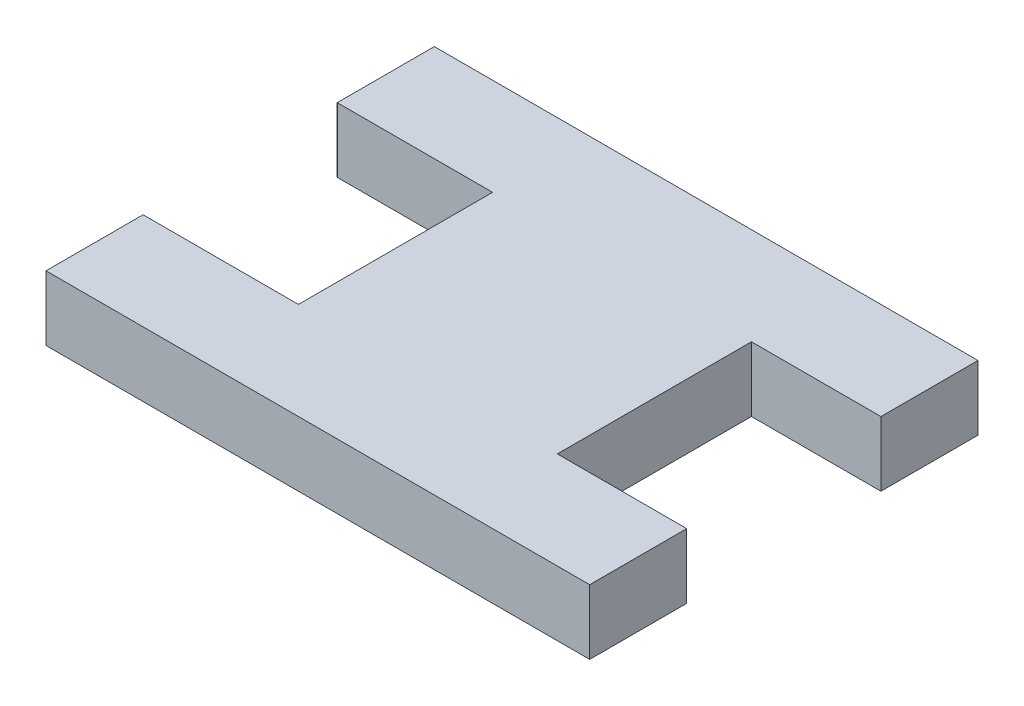
SolidWorks part; units mm, degrees
ref_plane "Front Plane" through (0, 0, 0) normal (0, 0, 1) x (1, 0, 0)
ref_plane "Top Plane" through (0, 0, 0) normal (0, 1, 0) x (1, 0, 0)
ref_plane "Right Plane" through (0, 0, 0) normal (1, 0, 0) x (0, 0, -1)
sketch "Sketch1" plane through (0, 0, 0) normal (0, 1, 0) x (1, 0, 0)
  line L1 (-47.5, -15) -> (47.5, -15)
  line L2 (-47.5, -15) -> (-47.5, 15)
  line L3 (-47.5, 15) -> (47.5, 15)
  line L4 (47.5, -15) -> (47.5, 15)
  line L5 (-47.5, -15) -> (47.5, 15) construction
  line L6 (-47.5, 15) -> (47.5, -15) construction
  circle A0 centre (-32.5, 0) radius 7
  circle A2 centre (-42.9, 0) radius 1
  circle A9 centre (-45.9, 0) radius 1
  circle A10 centre (-32.5, 10.4) radius 1
  circle A11 centre (-32.5, 13.4) radius 1
  circle A12 centre (-22.1, 0) radius 1
  circle A13 centre (-19.1, 0) radius 1
  circle A14 centre (-32.5, -10.4) radius 1
  circle A15 centre (-32.5, -13.4) radius 1
  point P0 (0, 0)
  point P26 (-32.5, 0)
  point P27 (-32.5, 0)
  dimension "D6" = 14
  dimension "D7" = 15
  dimension "D3" = 10.4
  dimension "D4" = 2
  dimension "D10" = 3
  dimension "D1" = 30
  dimension "D2" = 95
  dimension "D5" = 4
extrude "Boss-Extrude1" add sketch "Sketch1" along normal blind 5
sketch "Sketch3" plane through (0, 5, 0) normal (0, 1, 0) x (1, 0, 0)
  line L0 (-7.5, 5) -> (-2.5, 5)
  line L1 (-7.5, 5) -> (-7.5, -5)
  line L2 (-7.5, -5) -> (-2.5, -5)
  line L3 (-2.5, 5) -> (-2.5, -5)
  line L4 (-7.5, 5) -> (-2.5, -5) construction
  line L5 (-7.5, -5) -> (-2.5, 5) construction
  line L6 (-47.5, 15) -> (-47.5, -15) construction
  point P0 (-5, 0)
  dimension "D1" = 5
  dimension "D2" = 10
  dimension "D3" = 40
extrude "Cut-Extrude2" cut sketch "Sketch3" against normal blind 10
sketch "Sketch4" plane through (0, 5, 0) normal (0, 1, 0) x (1, 0, 0)
  line L0 (47.5, -15) -> (47.5, 15) construction
  line L1 (-3, -10) -> (37.5, -10) construction
  line L2 (-3, -10) -> (-3, 10) construction
  line L3 (-3, 10) -> (37.5, 10) construction
  line L4 (37.5, -10) -> (37.5, 10) construction
  line L5 (-3, -10) -> (37.5, 10) construction
  line L6 (-3, 10) -> (37.5, -10) construction
  line L7 (-2.5, 15) -> (-2.5, -15) construction
  line L8 (47.5, 15) -> (-47.5, 15) construction
  line L9 (-47.5, -15) -> (47.5, -15) construction
  circle A9 centre (-32.5, 0) radius 7 construction
  circle A10 centre (-32.5, 0) radius 7
  circle A15 centre (-32.5, -13.4) radius 1 construction
  circle A16 centre (-32.5, -10.4) radius 1 construction
  circle A17 centre (-42.9, 0) radius 1 construction
  circle A18 centre (-45.9, 0) radius 1 construction
  circle A19 centre (-32.5, 13.4) radius 1 construction
  circle A20 centre (-22.1, 0) radius 1 construction
  circle A21 centre (-19.1, 0) radius 1 construction
  circle A22 centre (-32.5, 10.4) radius 1 construction
  circle A23 centre (-32.5, -13.4) radius 1
  circle A24 centre (-32.5, -10.4) radius 1
  circle A25 centre (-42.9, 0) radius 1
  circle A26 centre (-45.9, 0) radius 1
  circle A27 centre (-32.5, 13.4) radius 1
  circle A28 centre (-22.1, 0) radius 1
  circle A29 centre (-19.1, 0) radius 1
  circle A30 centre (-32.5, 10.4) radius 1
  circle A31 centre (27.5, -13.4) radius 1
  circle A32 centre (27.5, -10.4) radius 1
  circle A33 centre (40.9, 0) radius 1
  circle A34 centre (37.9, 0) radius 1
  circle A35 centre (27.5, 0) radius 7
  circle A36 centre (27.5, 10.4) radius 1
  circle A37 centre (27.5, 13.4) radius 1
  circle A38 centre (17.1, 0) radius 1
  circle A39 centre (14.1, 0) radius 1
  point P0 (17.25, 0)
  point P29 (27.5, 0)
  dimension "D4" = 10
  dimension "D1" = 40.5
  dimension "D2" = 20
  dimension "D3" = 10
extrude "Cut-Extrude3" cut sketch "Sketch4" against normal blind 10
fillet "Fillet1" radius 10 4 edges at (47.5, 2.5, 15) (47.5, 2.5, -15) (-47.5, 2.5, 15) (-47.5, 2.5, -15)
sketch "Sketch5" plane through (0, 5, 0) normal (0, 1, 0) x (1, 0, 0)
  circle A0 centre (-7.5, 5) radius 2.05
  circle A1 centre (-2.5, 5) radius 2.05
  circle A2 centre (-2.5, -5) radius 2.05
  circle A3 centre (-7.5, -5) radius 2.05
  dimension "D1" = 4.1
extrude "Cut-Extrude4" cut sketch "Sketch5" against normal up to next
sketch "Sketch6" plane through (0, 5, 0) normal (0, 1, 0) x (1, 0, 0)
  line L0 (-22.5, 15) -> (19.5, 15)
  line L1 (37.5, 15) -> (-37.5, 15) construction
  line L2 (-22.5, 15) -> (-22.5, 7.5)
  line L3 (-22.5, 7.5) -> (-10.5, 7.5)
  line L4 (-10.5, 7.5) -> (-10.5, -7.5)
  line L5 (19.5, 15) -> (19.5, 7.5)
  line L6 (19.5, 7.5) -> (9.5, 7.5)
  line L7 (9.5, 7.5) -> (9.5, -7.5)
  line L8 (-10.5, 0) -> (9.5, 0) construction
  line L9 (19.5, -15) -> (19.5, -7.5)
  line L10 (19.5, -7.5) -> (9.5, -7.5)
  line L11 (-22.5, -7.5) -> (-10.5, -7.5)
  line L12 (-22.5, -15) -> (19.5, -15)
  line L13 (-22.5, -15) -> (-22.5, -7.5)
  line L14 (47.5, -5) -> (47.5, 5) construction
  line L16 (-47.5, 5) -> (-47.5, -5) construction
  point P5 (6.6705, 0)
  point P19 (-22.5, -8.3108)
  dimension "D1" = 25
  dimension "D2" = 12
  dimension "D3" = 15
  dimension "D4" = 28
  dimension "D5" = 10
extrude "Boss-Extrude2" add sketch "Sketch6" along normal blind 5
sketch "Sketch8" plane through (0, 0, 0) normal (0, -1, 0) x (1, 0, 0)
  line L4 (47.5, -5) -> (47.5, 5)
  line L5 (37.5, 15) -> (-37.5, 15)
  line L6 (-47.5, 5) -> (-47.5, -5)
  line L7 (-37.5, -15) -> (37.5, -15)
  line L8 (47.5, -5) -> (47.5, 5)
  line L9 (37.5, 15) -> (-37.5, 15)
  line L10 (-47.5, 5) -> (-47.5, -5)
  line L11 (-37.5, -15) -> (37.5, -15)
  arc A4 (47.5, 5) -> (37.5, 15) centre (37.5, 5) ccw
  arc A5 (-37.5, 15) -> (-47.5, 5) centre (-37.5, 5) ccw
  arc A6 (-47.5, -5) -> (-37.5, -15) centre (-37.5, -5) ccw
  arc A7 (37.5, -15) -> (47.5, -5) centre (37.5, -5) ccw
  arc A8 (47.5, 5) -> (37.5, 15) centre (37.5, 5) ccw
  arc A9 (-37.5, 15) -> (-47.5, 5) centre (-37.5, 5) ccw
  arc A10 (-47.5, -5) -> (-37.5, -15) centre (-37.5, -5) ccw
  arc A11 (37.5, -15) -> (47.5, -5) centre (37.5, -5) ccw
  dimension "D1" = 0
extrude "Cut-Extrude5" cut sketch "Sketch8" against normal blind 5
